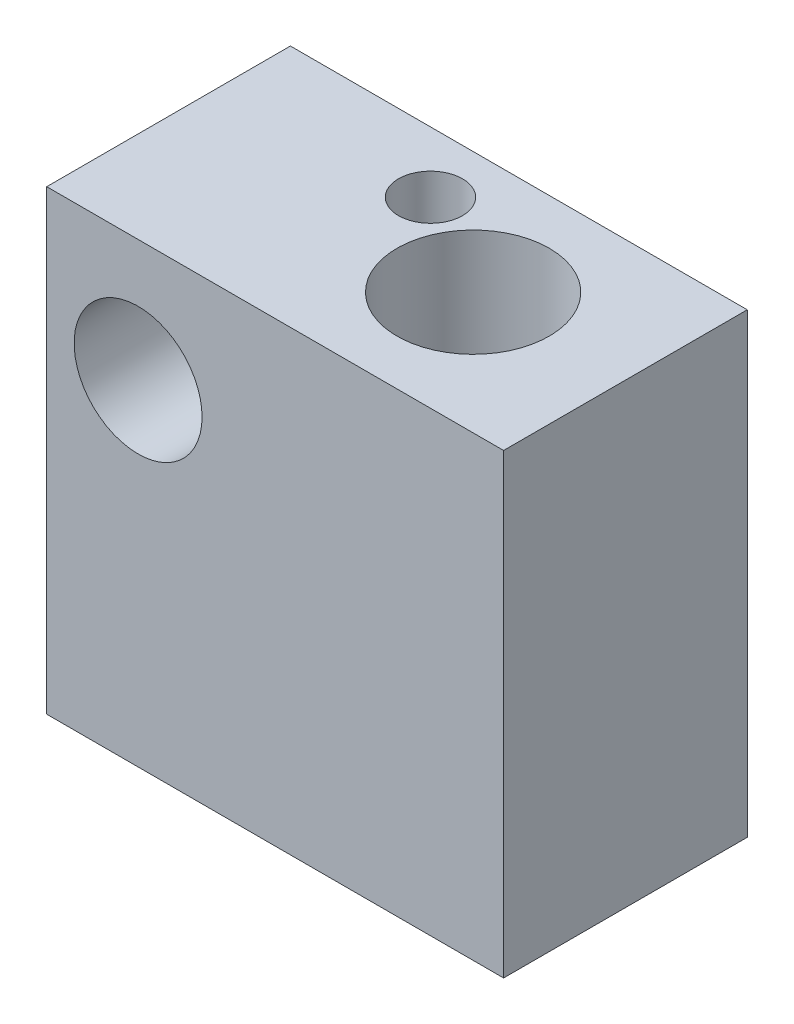
SolidWorks part; units mm, degrees
ref_plane "Front Plane" through (0, 0, 0) normal (0, 0, 1) x (1, 0, 0)
ref_plane "Top Plane" through (0, 0, 0) normal (0, 1, 0) x (1, 0, 0)
ref_plane "Right Plane" through (0, 0, 0) normal (1, 0, 0) x (0, 0, -1)
sketch "Sketch1" plane through (0, 0, 0) normal (0, 0, 1) x (1, 0, 0)
  line L1 (-3, 4) -> (12, 4)
  line L2 (-3, 4) -> (-3, -11)
  line L3 (-3, -11) -> (12, -11)
  line L4 (12, 4) -> (12, -11)
  circle A0 centre (0, 0) radius 2.1
  dimension "D1" = 4.2
  dimension "D2" = 3
  dimension "D3" = 15
  dimension "D4" = 15
  dimension "D5" = 4
extrude "Boss-Extrude1" add sketch "Sketch1" along normal blind 8
sketch "Sketch2" plane through (0, -11, 0) normal (0, -1, 0) x (1, 0, 0)
  line L0 (7, 4) -> (12, 4) construction
  line L1 (12, 8) -> (12, 0) construction
  circle A0 centre (7, 4) radius 2.5
  dimension "D1" = 5
  dimension "D2" = 7
extrude "Cut-Extrude1" cut sketch "Sketch2" against normal through all
sketch "Sketch3" plane through (0, -11, 0) normal (0, -1, 0) x (1, 0, 0)
  line L0 (-3, 0) -> (12, 0) construction
  line L1 (-3, 8) -> (-3, 0) construction
  circle A0 centre (3.6, 2) radius 1.05
  dimension "D1" = 2.1
  dimension "D3" = 6.6
  dimension "D2" = 2
extrude "Cut-Extrude2" cut sketch "Sketch3" against normal through all
